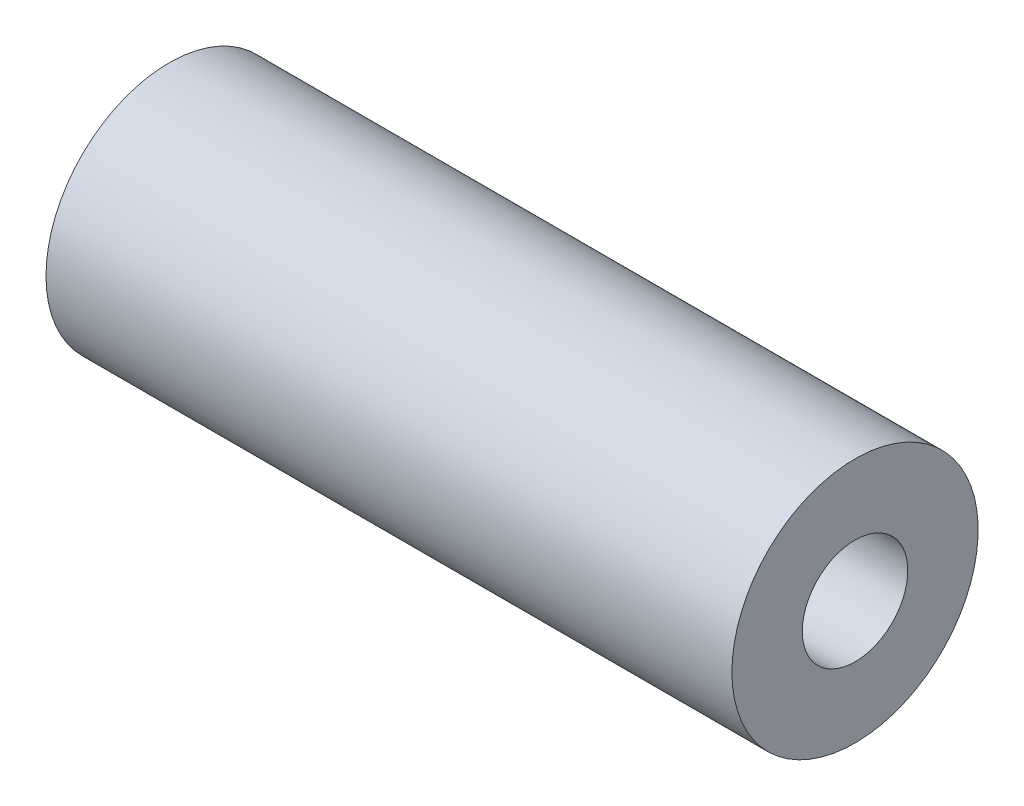
SolidWorks part; units mm, degrees
material "POM Acetal Copolymer"
ref_plane "Front Plane" through (0, 0, 0) normal (0, 0, 1) x (1, 0, 0)
ref_plane "Top Plane" through (0, 0, 0) normal (0, 1, 0) x (1, 0, 0)
ref_plane "Right Plane" through (0, 0, 0) normal (1, 0, 0) x (0, 0, -1)
sketch "Sketch1" plane through (0, 0, 0) normal (0, 0, 1) x (1, 0, 0)
  line L0 (-37.0032, 0) -> (19.5, 0) construction
  line L1 (-19.5, 7) -> (19.5, 7)
  line L2 (-19.5, 7) -> (-19.5, 3)
  line L3 (-19.5, 3) -> (19.5, 3)
  line L4 (19.5, 7) -> (19.5, 3)
  line L5 (19.5, 0) -> (19.5, 3) construction
  line L6 (0, 0) -> (0, 7) construction
  dimension "D1" = 6
  dimension "D2" = 39
  dimension "D3" = 14
revolve "Revolve1" add sketch "Sketch1" angle 360 about L0
